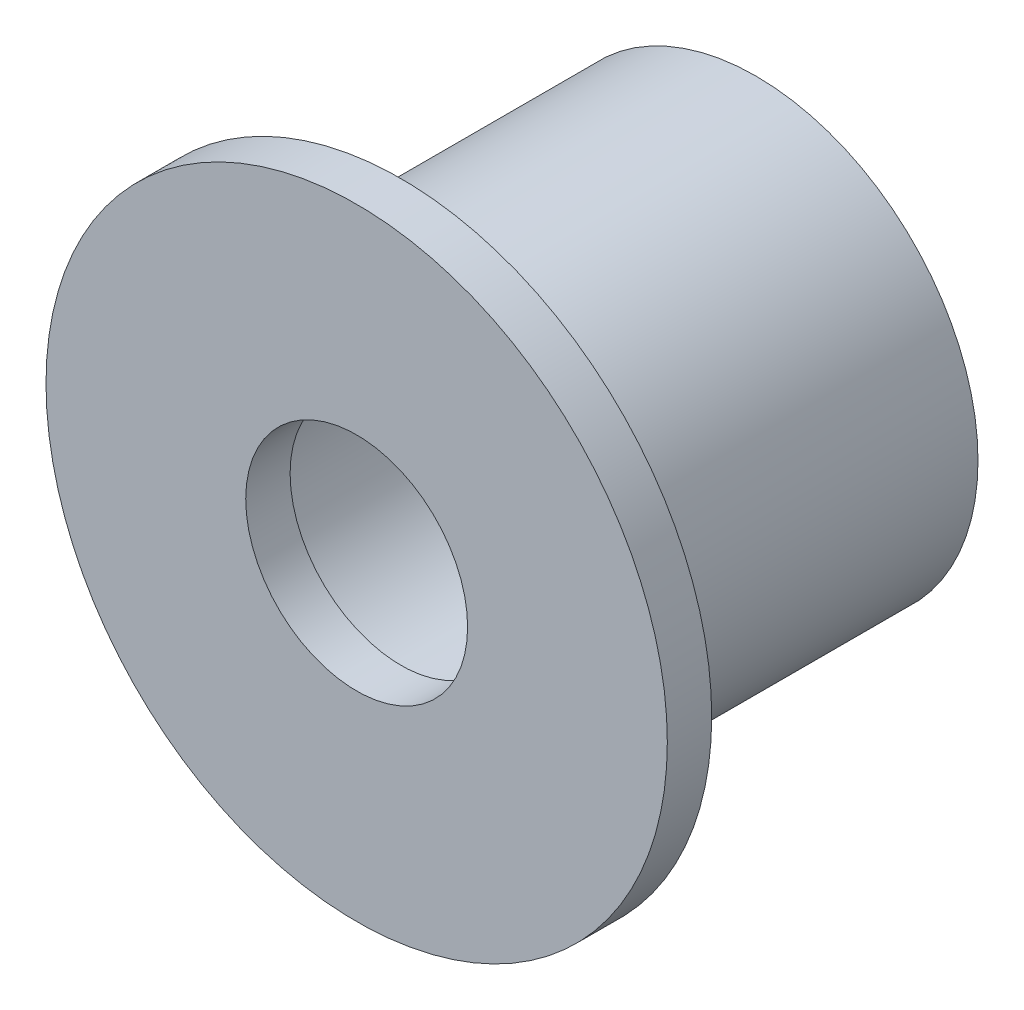
SolidWorks part; units mm, degrees
ref_plane "前视基准面" through (0, 0, 0) normal (0, 0, 1) x (1, 0, 0)
ref_plane "上视基准面" through (0, 0, 0) normal (0, 1, 0) x (1, 0, 0)
ref_plane "右视基准面" through (0, 0, 0) normal (1, 0, 0) x (0, 0, -1)
sketch "草图1" plane through (0, 0, 0) normal (0, 0, 1) x (1, 0, 0)
  circle A0 centre (0, 0) radius 7
  circle A1 centre (0, 0) radius 2.5
extrude "凸台-拉伸1" add sketch "草图1" along normal blind 1
sketch "草图2" plane through (0, 0, 0) normal (0, 0, -1) x (-1, 0, 0)
  circle A0 centre (0, 0) radius 5
  circle A1 centre (0, 0) radius 3
extrude "凸台-拉伸2" add sketch "草图2" along normal blind 8
